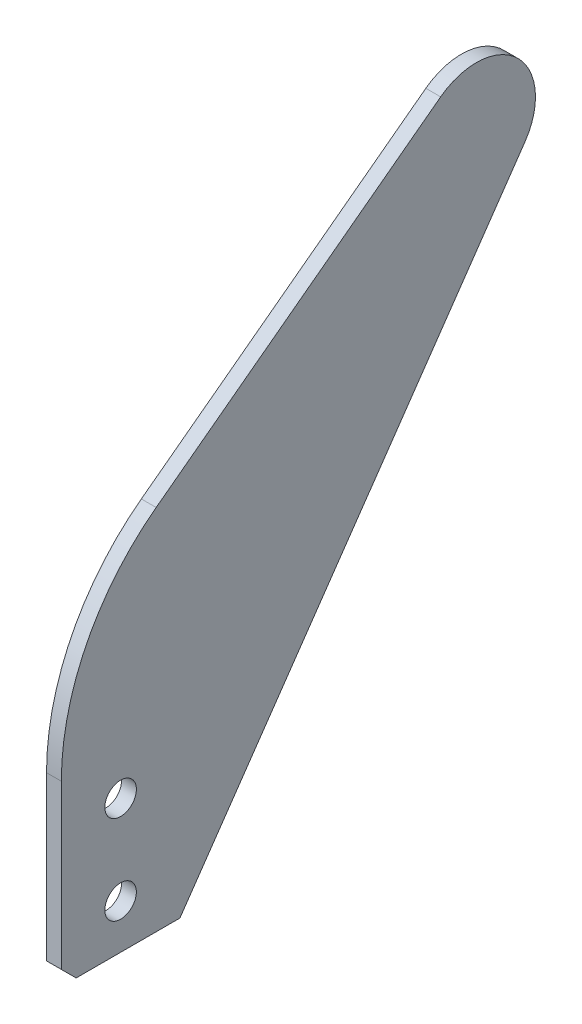
SolidWorks part; units mm, degrees
material "6061-T6 (SS)"
ref_plane "Front Plane" through (0, 0, 0) normal (0, 0, 1) x (1, 0, 0)
ref_plane "Top Plane" through (0, 0, 0) normal (0, 1, 0) x (1, 0, 0)
ref_plane "Right Plane" through (0, 0, 0) normal (1, 0, 0) x (0, 0, -1)
sketch "Sketch1" plane through (0, 0, 0) normal (1, 0, 0) x (0, 0, -1)
  line L0 (0, 0) -> (0, 38.1)
  line L1 (0, 0) -> (25.4, 0)
  line L2 (25.4, 0) -> (99.3502, 107.0832)
  line L4 (81.28, 124.46) -> (20.32, 78.74)
  arc A0 (20.32, 78.74) -> (0, 38.1) centre (50.8, 38.1) ccw
  arc A1 (81.28, 124.46) -> (99.3502, 107.0832) centre (88.9, 114.3) cw
  circle A2 centre (12.7, 9.525) radius 3.3782
  circle A3 centre (12.7, 28.575) radius 3.3782
  point P14 (12.7, 0)
  dimension "D2" = 50.8
  dimension "D3" = 12.7
  dimension "D7" = 6.7564
  dimension "D8" = 12.7
  dimension "D9" = 9.525
  dimension "D1" = 25.4
  dimension "D4" = 88.9
  dimension "D5" = 114.3
  dimension "D6" = 38.1
  dimension "D10" = 9.525
extrude "Boss-Extrude1" add sketch "Sketch1" along normal blind 3.175
chamfer "Chamfer1" distance 3.175 angle 45 1 edges at (1.5875, 0, 0)
